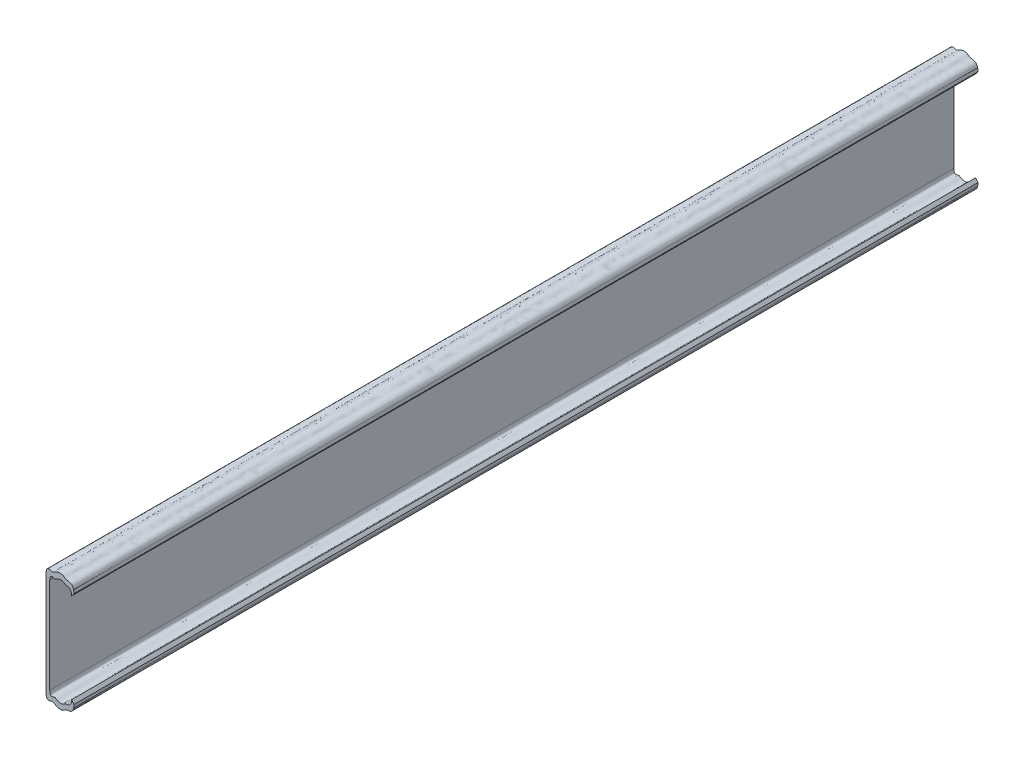
SolidWorks part; units mm, degrees
material "6061 Alloy"
ref_plane "Front Plane" through (0, 0, 0) normal (0, 0, 1) x (1, 0, 0)
ref_plane "Top Plane" through (0, 0, 0) normal (0, 1, 0) x (1, 0, 0)
ref_plane "Right Plane" through (0, 0, 0) normal (1, 0, 0) x (0, 0, -1)
sketch "Sketch1" plane through (0, 0, 0) normal (0, 0, 1) x (1, 0, 0)
  line L0 (1.4303, 3918.1704) -> (1.4303, 3954.729)
  line L1 (0, 3956.1915) -> (0, 3916.7079)
  spline S0 degree 3 poles (1.4303, 3954.729) (1.4923, 3955.7775) (1.6707, 3956.0853) (1.9528, 3956.2434) (2.0122, 3956.2646) (2.2569, 3956.3286) (2.4564, 3956.3207) (2.7579, 3956.2594) (2.8675, 3956.2205) (3.0656, 3956.1422) (3.1573, 3956.1046) (3.353, 3956.0751) (3.4576, 3956.0848) (3.827, 3956.2366) (4.1394, 3956.4769) (4.6798, 3956.7324) (4.8724, 3956.7987) (5.2595, 3956.8913) (5.4539, 3956.9177) (5.8211, 3956.9293) (5.9922, 3956.9136) (6.3808, 3956.8295) (6.5805, 3956.7396) (6.8008, 3956.5897) (6.8513, 3956.5495) (7.0576, 3956.3849) (7.2245, 3956.2529) (7.6941, 3956.1293) (7.8335, 3956.1044) (7.9967, 3956.0819) knots 0 0 0 0 0.125 0.125 0.15625 0.15625 0.25 0.25 0.3125 0.3125 0.375 0.375 0.4375 0.4375 0.5625 0.5625 0.625 0.625 0.6875 0.6875 0.75 0.75 0.84375 0.84375 0.875 0.875 0.96875 0.96875 1 1 1 1
  spline S1 degree 3 poles (7.9967, 3916.8175) (7.8335, 3916.795) (7.6941, 3916.7701) (7.2245, 3916.6465) (7.0576, 3916.5145) (6.8513, 3916.3499) (6.8008, 3916.3097) (6.5805, 3916.1598) (6.3808, 3916.0699) (5.9922, 3915.9858) (5.8211, 3915.9701) (5.4539, 3915.9817) (5.2595, 3916.0081) (4.8724, 3916.1007) (4.6798, 3916.167) (4.1394, 3916.4225) (3.827, 3916.6628) (3.4576, 3916.8146) (3.353, 3916.8243) (3.1573, 3916.7948) (3.0656, 3916.7572) (2.8675, 3916.6789) (2.7579, 3916.64) (2.4564, 3916.5787) (2.2569, 3916.5708) (2.0122, 3916.6348) (1.9528, 3916.656) (1.6707, 3916.8141) (1.4923, 3917.1219) (1.4303, 3918.1704) knots 0 0 0 0 0.03125 0.03125 0.125 0.125 0.15625 0.15625 0.25 0.25 0.3125 0.3125 0.375 0.375 0.4375 0.4375 0.5625 0.5625 0.625 0.625 0.6875 0.6875 0.75 0.75 0.84375 0.84375 0.875 0.875 1 1 1 1
  spline S2 degree 3 poles (0, 3916.7079) (0.088, 3915.217) (0.36, 3914.8944) (1.0287, 3914.6285) (1.426, 3914.6674) (2.0597, 3914.8618) (2.2832, 3915.025) (2.7602, 3914.9201) (2.9457, 3914.8187) (3.3641, 3914.5669) (3.5966, 3914.4177) (4.1003, 3914.1642) (4.3735, 3914.0651) (4.9238, 3913.9317) (5.2007, 3913.8964) (5.9749, 3913.8882) (6.4024, 3914.0202) (6.8144, 3914.2728) (6.8893, 3914.3279) (7.2178, 3914.5871) (7.4664, 3914.8164) (8.2929, 3914.9575) (8.4066, 3914.9721) (9.2507, 3915.0909) (10.2169, 3915.2813) (10.5629, 3916.8175) knots 0 0 0 0 0.125 0.125 0.25 0.25 0.375 0.375 0.4375 0.4375 0.5 0.5 0.5625 0.5625 0.625 0.625 0.75 0.75 0.78125 0.78125 0.890625 0.890625 0.90625 0.90625 1 1 1 1
  spline S3 degree 3 poles (10.5629, 3956.0819) (10.2169, 3957.6181) (9.2507, 3957.8085) (8.4066, 3957.9273) (8.2929, 3957.9419) (7.4664, 3958.083) (7.2178, 3958.3123) (6.8893, 3958.5715) (6.8144, 3958.6266) (6.4024, 3958.8792) (5.9749, 3959.0112) (5.2007, 3959.003) (4.9238, 3958.9677) (4.3735, 3958.8343) (4.1003, 3958.7352) (3.5966, 3958.4817) (3.3641, 3958.3325) (2.9457, 3958.0807) (2.7602, 3957.9793) (2.2832, 3957.8744) (2.0597, 3958.0376) (1.426, 3958.232) (1.0287, 3958.2709) (0.36, 3958.005) (0.088, 3957.6824) (0, 3956.1915) knots 0 0 0 0 0.09375 0.09375 0.109375 0.109375 0.21875 0.21875 0.25 0.25 0.375 0.375 0.4375 0.4375 0.5 0.5 0.5625 0.5625 0.625 0.625 0.75 0.75 0.875 0.875 1 1 1 1
  spline S4 degree 3 poles (10.6926, 3954.8106) (10.6919, 3954.8622) (10.6905, 3954.9632) (10.6847, 3955.1173) (10.6763, 3955.2678) (10.6597, 3955.4783) (10.63, 3955.7467) (10.5846, 3955.9736) (10.5629, 3956.0819) knots 0 0 0 0 0.133576 0.261602 0.383626 0.499199 0.760926 1 1 1 1
  spline S5 degree 3 poles (9.7722, 3953.6517) (9.9024, 3953.8157) (10.0416, 3953.991) (10.3506, 3954.38) (10.5159, 3954.5881) (10.6926, 3954.8106) knots 0 0 0 0 0.5 0.5 1 1 1 1
  spline S6 degree 3 poles (7.9967, 3956.0819) (8.0881, 3956.0693) (8.2728, 3956.044) (8.548, 3955.9842) (8.8073, 3955.8876) (9.1144, 3955.706) (9.3935, 3955.3952) (9.5812, 3954.9939) (9.668, 3954.6744) (9.713, 3954.4321) (9.7438, 3954.21) (9.766, 3953.9385) (9.77, 3953.752) (9.7722, 3953.6517) knots 0 0 0 0 0.060951 0.123017 0.186645 0.24715 0.371687 0.497525 0.623449 0.683912 0.749157 0.865106 1 1 1 1
  spline S7 degree 3 poles (10.6926, 3918.0888) (10.5159, 3918.3113) (10.3506, 3918.5194) (10.0416, 3918.9084) (9.9024, 3919.0837) (9.7722, 3919.2477) knots 0 0 0 0 0.5 0.5 1 1 1 1
  spline S8 degree 3 poles (10.5629, 3916.8175) (10.5742, 3916.8705) (10.5973, 3916.9791) (10.6243, 3917.1434) (10.6472, 3917.3125) (10.6695, 3917.5276) (10.6871, 3917.7923) (10.6907, 3917.9869) (10.6926, 3918.0888) knots 0 0 0 0 0.11653 0.239104 0.36735 0.500883 0.738425 1 1 1 1
  spline S9 degree 3 poles (9.7722, 3919.2477) (9.7714, 3919.1969) (9.7698, 3919.0982) (9.7627, 3918.9437) (9.752, 3918.7926) (9.7361, 3918.6338) (9.713, 3918.4673) (9.668, 3918.225) (9.5812, 3917.9055) (9.3935, 3917.5042) (9.1144, 3917.1934) (8.8074, 3917.0118) (8.5481, 3916.9152) (8.2728, 3916.8554) (8.0881, 3916.8301) (7.9967, 3916.8175) knots 0 0 0 0 0.069471 0.134905 0.195584 0.250878 0.316109 0.37658 0.502498 0.62833 0.752861 0.813354 0.876989 0.939052 1 1 1 1
extrude "Boss-Extrude1" add sketch "Sketch1" along normal blind 346
sketch "Sketch2" plane through (0, 0, 346) normal (0, 0, 1) x (1, 0, 0)
  line L0 (0, 3936.4497) -> (1.4303, 3936.4497)
  line L1 (0, 3956.1915) -> (0, 3916.7079) construction
  line L2 (1.4303, 3918.1704) -> (1.4303, 3954.729) construction
ref_plane "Plane2" through (0, 3936.4497, 0) normal (0, -1, 0) x (1, 0, 0)
